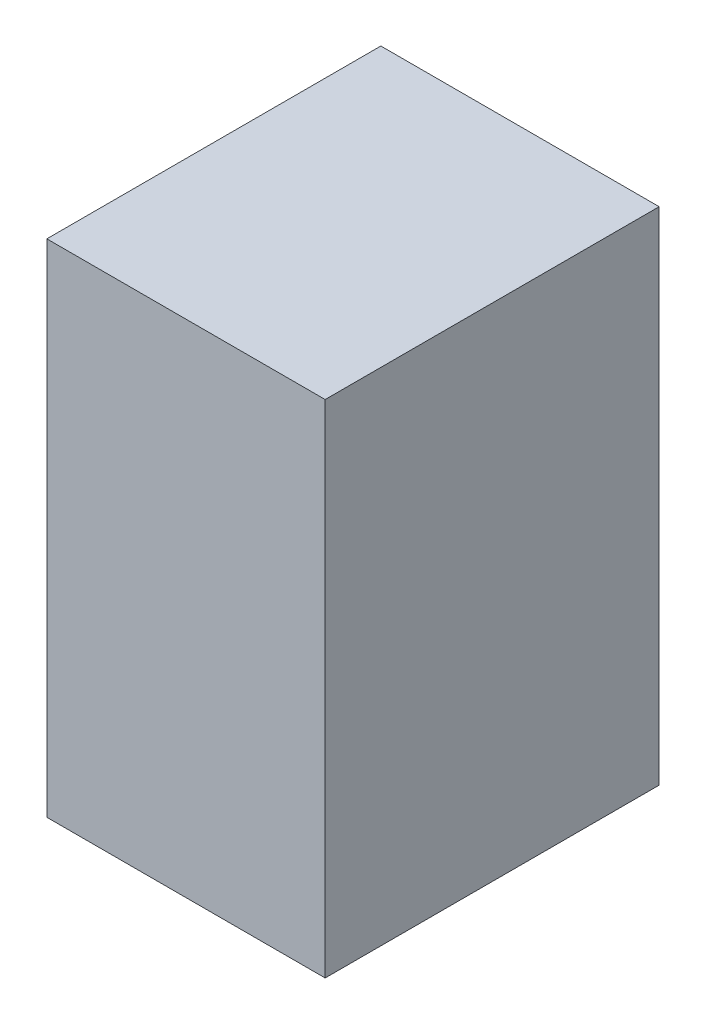
SolidWorks part; units mm, degrees
ref_plane "Front Plane" through (0, 0, 0) normal (1, 0, 0) x (0, 1, 0)
ref_plane "Top Plane" through (0, 0, 0) normal (0, 0, 1) x (0, 1, 0)
ref_plane "Right Plane" through (0, 0, 0) normal (0, 1, 0) x (-1, 0, 0)
sketch "Sketch2" plane through (0, 0, 0) normal (1, 0, 0) x (0, 1, 0)
  line L1 (-22.5, -15) -> (22.5, -15)
  line L2 (-22.5, -15) -> (-22.5, 15)
  line L3 (-22.5, 15) -> (22.5, 15)
  line L4 (22.5, -15) -> (22.5, 15)
  line L5 (-22.5, -15) -> (22.5, 15) construction
  line L6 (-22.5, 15) -> (22.5, -15) construction
  point P0 (0, 0)
  dimension "D1" = 45
  dimension "D2" = 30
extrude "Boss-Extrude1" add sketch "Sketch2" along normal blind 25
